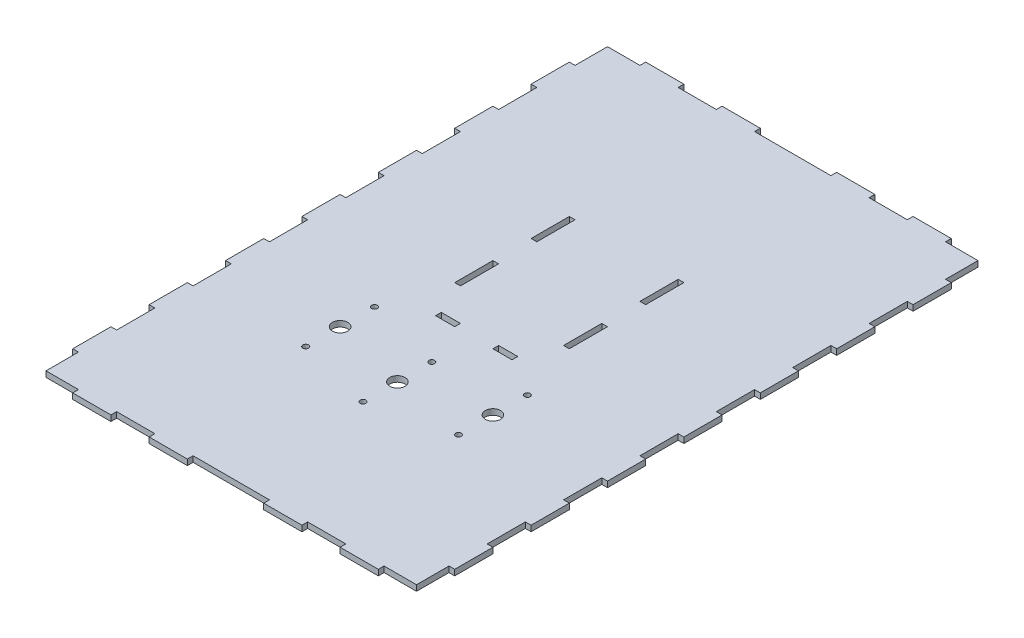
SolidWorks part; units mm, degrees
ref_plane "Front Plane" through (0, 0, 0) normal (0, 0, 1) x (1, 0, 0)
ref_plane "Top Plane" through (0, 0, 0) normal (0, 1, 0) x (1, 0, 0)
ref_plane "Right Plane" through (0, 0, 0) normal (1, 0, 0) x (0, 0, -1)
sketch "Sketch1" plane through (0, 0, 0) normal (0, 1, 0) x (1, 0, 0)
  line L1 (100, 150) -> (-100, 150)
  line L2 (100, 150) -> (100, -150)
  line L3 (100, -150) -> (-100, -150)
  line L4 (-100, 150) -> (-100, -150)
  line L5 (100, 150) -> (-100, -150) construction
  line L6 (100, -150) -> (-100, 150) construction
  point P0 (0, 0)
extrude "Boss-Extrude1" add sketch "Sketch1" along normal blind 3
sketch "Sketch2" plane through (0, 3, 0) normal (0, 1, 0) x (1, 0, 0)
  line L1 (-27, 0) -> (-27, 20)
  line L2 (30, 0) -> (30, 20)
  line L4 (-30, 0) -> (-30, 20)
  line L5 (27, 0) -> (27, 20)
  line L6 (20, -17) -> (10, -17)
  line L7 (20, -20) -> (10, -20)
  line L8 (30, 0) -> (27, 0)
  line L9 (30, 20) -> (27, 20)
  line L10 (30, 40) -> (27, 40)
  line L11 (30, 60) -> (27, 60)
  line L12 (-27, 60) -> (-30, 60)
  line L13 (-27, 40) -> (-30, 40)
  line L14 (-27, 20) -> (-30, 20)
  line L15 (-27, 0) -> (-30, 0)
  line L16 (-20, -20) -> (-20, -17)
  line L17 (-10, -20) -> (-10, -17)
  line L18 (-30, 40) -> (-30, 60)
  line L19 (10, -20) -> (10, -17)
  line L20 (20, -20) -> (20, -17)
  line L23 (-10, -17) -> (-20, -17)
  line L26 (30, 80) -> (-30, 80) construction
  line L27 (27, 77) -> (-27, 77) construction
  line L28 (-27, -17) -> (-27, 77) construction
  line L29 (-30, -20) -> (-30, 80) construction
  line L30 (27, -17) -> (27, 77) construction
  line L31 (30, -20) -> (30, 80) construction
  line L32 (27, -17) -> (-27, -17) construction
  line L33 (30, -20) -> (-30, -20) construction
  line L36 (-10, -20) -> (-20, -20)
  line L37 (0, -20) -> (0, -17) [skipped]
  line L38 (-27, 40) -> (-27, 60)
  line L39 (27, 40) -> (27, 60)
  line L40 (30, 40) -> (30, 60)
  point P0 (0, 0)
  dimension "D1" = 5
extrude "Cut-Extrude1" cut sketch "Sketch2" against normal blind 3
sketch "Sketch3" plane through (0, 3, 0) normal (0, 1, 0) x (1, 0, 0)
  line L0 (100, 130) -> (97, 130)
  line L1 (100, 110) -> (97, 110)
  line L2 (100, 90) -> (97, 90)
  line L3 (100, 70) -> (97, 70)
  line L4 (-100, 150) -> (-100, -150)
  line L5 (-100, -150) -> (100, -150)
  line L6 (100, -150) -> (100, 150)
  line L7 (100, 150) -> (-100, 150)
  line L8 (-100, 150) -> (-100, 130)
  line L9 (-100, -150) -> (-80, -150)
  line L10 (100, -150) -> (100, -130)
  line L11 (100, 150) -> (80, 150)
  line L12 (100, 50) -> (97, 50)
  line L13 (100, 30) -> (97, 30)
  line L14 (100, 10) -> (97, 10)
  line L15 (100, -10) -> (97, -10)
  line L16 (-97, 147) -> (-97, -147)
  line L17 (-97, -147) -> (97, -147)
  line L18 (97, -147) -> (97, 147)
  line L19 (97, 147) -> (-97, 147)
  line L20 (-97, 147) -> (-97, 130)
  line L21 (-97, -147) -> (-80, -147)
  line L22 (97, -147) -> (97, -130)
  line L23 (97, 147) -> (80, 147)
  line L24 (100, -30) -> (97, -30)
  line L25 (100, -50) -> (97, -50)
  line L26 (100, -70) -> (97, -70)
  line L27 (100, -90) -> (97, -90)
  line L28 (100, -110) -> (97, -110)
  line L29 (100, -130) -> (97, -130)
  line L30 (-97, 130) -> (-100, 130)
  line L31 (-97, 110) -> (-100, 110)
  line L32 (-97, 90) -> (-100, 90)
  line L33 (-97, 70) -> (-100, 70)
  line L34 (-97, 50) -> (-100, 50)
  line L35 (-97, 30) -> (-100, 30)
  line L36 (-97, 10) -> (-100, 10)
  line L37 (-97, -10) -> (-100, -10)
  line L38 (-97, -30) -> (-100, -30)
  line L39 (-97, -50) -> (-100, -50)
  line L40 (-97, -70) -> (-100, -70)
  line L41 (-97, -90) -> (-100, -90)
  line L42 (-97, -110) -> (-100, -110)
  line L43 (-97, -130) -> (-100, -130)
  line L44 (100, -110) -> (100, -90)
  line L45 (97, -110) -> (97, -90)
  line L46 (100, -70) -> (100, -50)
  line L47 (97, -70) -> (97, -50)
  line L48 (100, 130) -> (100, 150)
  line L49 (97, 130) -> (97, 147)
  line L50 (100, 90) -> (100, 110)
  line L51 (97, 90) -> (97, 110)
  line L52 (100, 50) -> (100, 70)
  line L53 (97, 50) -> (97, 70)
  line L54 (100, -30) -> (100, -10)
  line L55 (97, -30) -> (97, -10)
  line L56 (100, 10) -> (100, 30)
  line L57 (97, 10) -> (97, 30)
  line L58 (-97, 110) -> (-97, 90)
  line L59 (-100, 110) -> (-100, 90)
  line L60 (-97, 70) -> (-97, 50)
  line L61 (-100, 70) -> (-100, 50)
  line L62 (-97, 30) -> (-97, 10)
  line L63 (-100, 30) -> (-100, 10)
  line L64 (-97, -10) -> (-97, -30)
  line L65 (-100, -10) -> (-100, -30)
  line L66 (-97, -50) -> (-97, -70)
  line L67 (-100, -50) -> (-100, -70)
  line L68 (-97, -90) -> (-97, -110)
  line L69 (-100, -90) -> (-100, -110)
  line L70 (-97, -130) -> (-97, -147)
  line L71 (-100, -130) -> (-100, -150)
  line L72 (-80, 150) -> (-80, 147)
  line L73 (-60, 150) -> (-60, 147)
  line L74 (-40, 150) -> (-40, 147)
  line L75 (-20, 150) -> (-20, 147)
  line L76 (80, -150) -> (80, -147)
  line L77 (20, 150) -> (20, 147)
  line L78 (40, 150) -> (40, 147)
  line L79 (60, 150) -> (60, 147)
  line L80 (80, 150) -> (80, 147)
  line L81 (60, 150) -> (40, 150)
  line L82 (60, 147) -> (40, 147)
  line L83 (-80, 150) -> (-100, 150)
  line L84 (-80, 147) -> (-97, 147)
  line L85 (-40, 150) -> (-60, 150)
  line L86 (-40, 147) -> (-60, 147)
  line L87 (20, 150) -> (-20, 150)
  line L88 (20, 147) -> (-20, 147)
  line L89 (0, 150) -> (0, 147) [skipped]
  line L90 (60, -150) -> (60, -147)
  line L91 (40, -150) -> (40, -147)
  line L92 (20, -150) -> (20, -147)
  line L94 (-20, -150) -> (-20, -147)
  line L95 (-40, -150) -> (-40, -147)
  line L96 (-60, -150) -> (-60, -147)
  line L97 (-80, -150) -> (-80, -147)
  line L98 (80, -147) -> (97, -147)
  line L99 (80, -150) -> (100, -150)
  line L100 (-60, -147) -> (-40, -147)
  line L101 (-60, -150) -> (-40, -150)
  line L102 (-20, -150) -> (20, -150)
  line L103 (-20, -147) -> (20, -147)
  line L104 (40, -147) -> (60, -147)
  line L105 (40, -150) -> (60, -150)
  line L106 (0, -147) -> (0, -130) [skipped]
  dimension "D1" = 0
  dimension "D2" = 3
  dimension "D3" = 15
extrude "Cut-Extrude2" cut sketch "Sketch3" against normal blind 3
sketch "Sketch4" plane through (0, 3, 0) normal (0, 1, 0) x (1, 0, 0)
  circle A0 centre (0, -60) radius 4
  circle A1 centre (40, -50) radius 4
  circle A2 centre (-40, -50) radius 4
  circle A3 centre (40, -32) radius 1.5
  circle A4 centre (40, -68) radius 1.5
  circle A5 centre (0, -42) radius 1.5
  circle A6 centre (0, -78) radius 1.5
  circle A7 centre (-40, -32) radius 1.5
  circle A8 centre (-40, -68) radius 1.5
  point P5 (0, -60)
extrude "Cut-Extrude3" cut sketch "Sketch4" against normal blind 3
